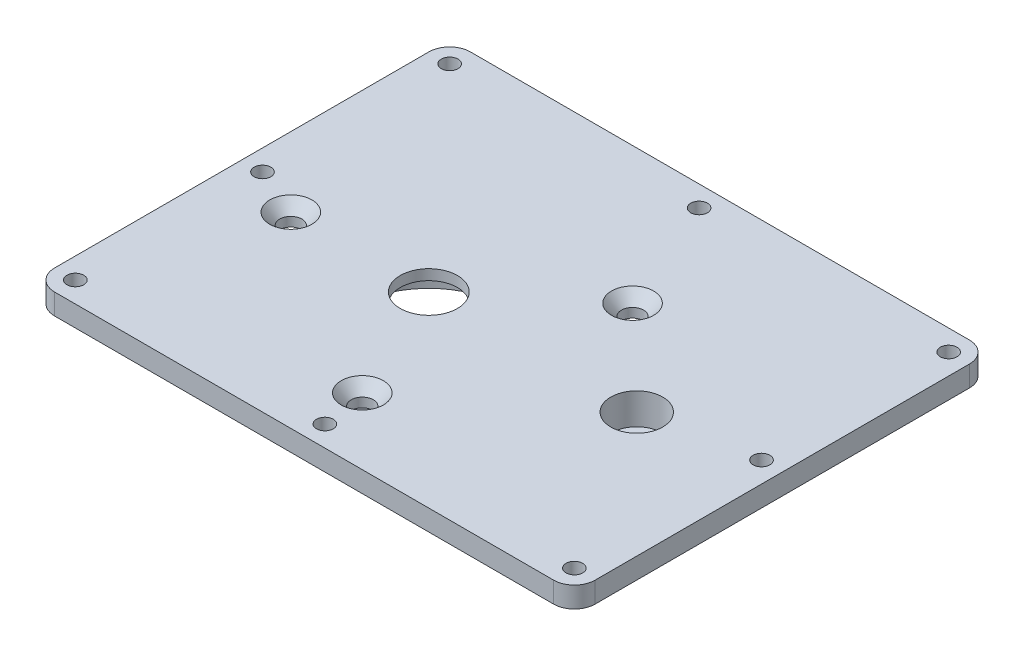
SolidWorks part; units mm, degrees
ref_plane "Front Plane" through (0, 0, 0) normal (0, 0, 1) x (1, 0, 0)
ref_plane "Top Plane" through (0, 0, 0) normal (0, 1, 0) x (1, 0, 0)
ref_plane "Right Plane" through (0, 0, 0) normal (1, 0, 0) x (0, 0, -1)
sketch "Sketch1" plane through (0, 0, 0) normal (0, 1, 0) x (1, 0, 0)
  line L1 (82.55, -63.5) -> (-82.55, -63.5)
  line L2 (82.55, -63.5) -> (82.55, 63.5)
  line L3 (82.55, 63.5) -> (-82.55, 63.5)
  line L4 (-82.55, -63.5) -> (-82.55, 63.5)
  line L5 (82.55, -63.5) -> (-82.55, 63.5) construction
  line L6 (82.55, 63.5) -> (-82.55, -63.5) construction
  circle A0 centre (-19.05, -6.35) radius 7.1438
  circle A1 centre (44.45, -6.35) radius 7.9375
  point P0 (0, 0)
  dimension "D5" = 14.2875
  dimension "D6" = 15.875
  dimension "D1" = 165.1
  dimension "D2" = 127
  dimension "D3" = 63.5
  dimension "D4" = 63.5
  dimension "D7" = 57.15
extrude "Boss-Extrude1" add sketch "Sketch1" along normal blind 6.35
sketch "Sketch2" plane through (0, 6.35, 0) normal (0, 1, 0) x (1, 0, 0)
  circle A0 centre (44.45, -6.35) radius 7.9375 construction
  circle A1 centre (-19.05, -6.35) radius 7.1438 construction
  circle A2 centre (44.45, -6.35) radius 7.9375
  circle A3 centre (-19.05, -6.35) radius 7.1438
  circle A4 centre (-19.05, -6.35) radius 28.575
  circle A5 centre (44.45, -6.35) radius 12.7
  dimension "D1" = 25.4
  dimension "D2" = 57.15
extrude "Boss-Extrude2" add sketch "Sketch2" against normal blind 15.875
sketch "Sketch3" plane through (0, 6.35, 0) normal (0, -1, 0) x (1, 0, 0)
  circle A0 centre (-19.05, 6.35) radius 8.7313
  dimension "D1" = 17.4625
extrude "Cut-Extrude1" cut sketch "Sketch3" along normal blind 3.175
sketch "Sketch4" plane through (0, -9.525, 0) normal (0, -1, 0) x (-1, 0, 0)
  circle A0 centre (19.05, -6.35) radius 23.8125
  dimension "D1" = 47.625
extrude "Cut-Extrude2" cut sketch "Sketch4" against normal blind 12.7
sketch "Sketch5" plane through (0, 0, 0) normal (0, -1, 0) x (1, 0, 0)
  circle A0 centre (44.45, 6.35) radius 7.9375 construction
  circle A1 centre (44.45, 6.35) radius 7.9375
extrude "Boss-Extrude4" add sketch "Sketch5" along normal up to surface (6.35 mm away) from offset 3.175 contours A1 up to face at (44.45, -9.525, 14.2875)
sketch "Sketch6" plane through (0, 6.35, 0) normal (0, 1, 0) x (1, 0, 0)
  circle A0 centre (-2.54, -43.18) radius 3.175
  circle A1 centre (-61.2557, -6.2912) radius 3.175
  circle A2 centre (15.0156, 21.8003) radius 3.175
  circle A5 centre (-19.05, -6.35) radius 8.7313 construction
  circle A6 centre (-19.05, -6.35) radius 8.7313
  dimension "D3" = 6.35
  dimension "D1" = 16.51
  dimension "D2" = 36.83
  dimension "D4" = 42.2057
  dimension "D5" = 69.342
  dimension "D6" = 81.28
  dimension "D7" = 67.31
hole_wizard "CSK for 1/4 Flat Head Machine Screw1" positions "Sketch7" profile "Sketch8" countersink size "1/4" standard "ANSI Inch" end condition through all
sketch "Sketch7" plane through (0, 6.35, 0) normal (0, 1, 0) x (1, 0, 0)
  point P0 (-61.2557, -6.2912)
  point P3 (15.0156, 21.8003)
  point P6 (-2.54, -43.18)
sketch "Sketch8" plane through (-61.2557, 6.35, 6.2912) normal (1, 0, 0) x (0, 0, 1)
  line L0 (0, 0) -> (0, 15.875)
  line L1 (0, 15.875) -> (3.3782, 15.875)
  line L2 (3.3782, 15.875) -> (3.3782, 3.5209)
  line L3 (3.3782, 3.5209) -> (6.4389, 0)
  line L5 (6.4389, 0) -> (0, 0)
  line L6 (-3.3782, 3.5209) -> (-6.4389, 0) construction
  line L11 (0, -6.35) -> (0, 107.95) construction
  dimension "Thru Hole Dia." = 6.7564
  dimension "Thru Hole Depth" = 15.875
  dimension "Near C'Sink Dia." = 12.8778
  dimension "Near C'Sink Angle" = 82
fillet "Fillet1" radius 6.35 4 edges at (82.55, 3.175, -63.5) (82.55, 3.175, 63.5) (-82.55, 3.175, 63.5) (-82.55, 3.175, -63.5)
hole_wizard "#10 Clearance Hole1" positions "Sketch9" profile "Sketch10" hole size "#10" standard "ANSI Inch" end condition through all
sketch "Sketch9" plane through (0, 6.35, 0) normal (0, 1, 0) x (1, 0, 0)
  line L0 (-76.2, 57.15) -> (76.2, 57.15)
  line L1 (76.2, 57.15) -> (76.2, -57.15)
  line L2 (76.2, -57.15) -> (-76.2, -57.15)
  line L3 (-76.2, -57.15) -> (-76.2, 57.15)
  point P0 (-76.2, -57.15)
  point P3 (-76.2, 57.15)
  point P6 (76.2, 57.15)
  point P9 (76.2, -57.15)
  point P21 (0, 57.15)
  point P23 (0, -57.15)
  point P32 (-76.2, 0)
  point P36 (76.2, 0)
  point P40 (76.2, -15.8456)
  point P41 (0, 0)
  point P42 (-76.2, 0)
  point P43 (-76.2, 12.65)
sketch "Sketch10" plane through (-76.2, 6.35, 57.15) normal (1, 0, 0) x (0, 0, 1)
  line L0 (0, 0) -> (0, 15.875)
  line L1 (0, 15.875) -> (2.5527, 15.875)
  line L2 (2.5527, 15.875) -> (2.5527, 0)
  line L5 (2.5527, 0) -> (0, 0)
  line L11 (0, -6.35) -> (0, 107.95) construction
  dimension "Thru Hole Dia." = 5.1054
  dimension "Thru Hole Depth" = 15.875
